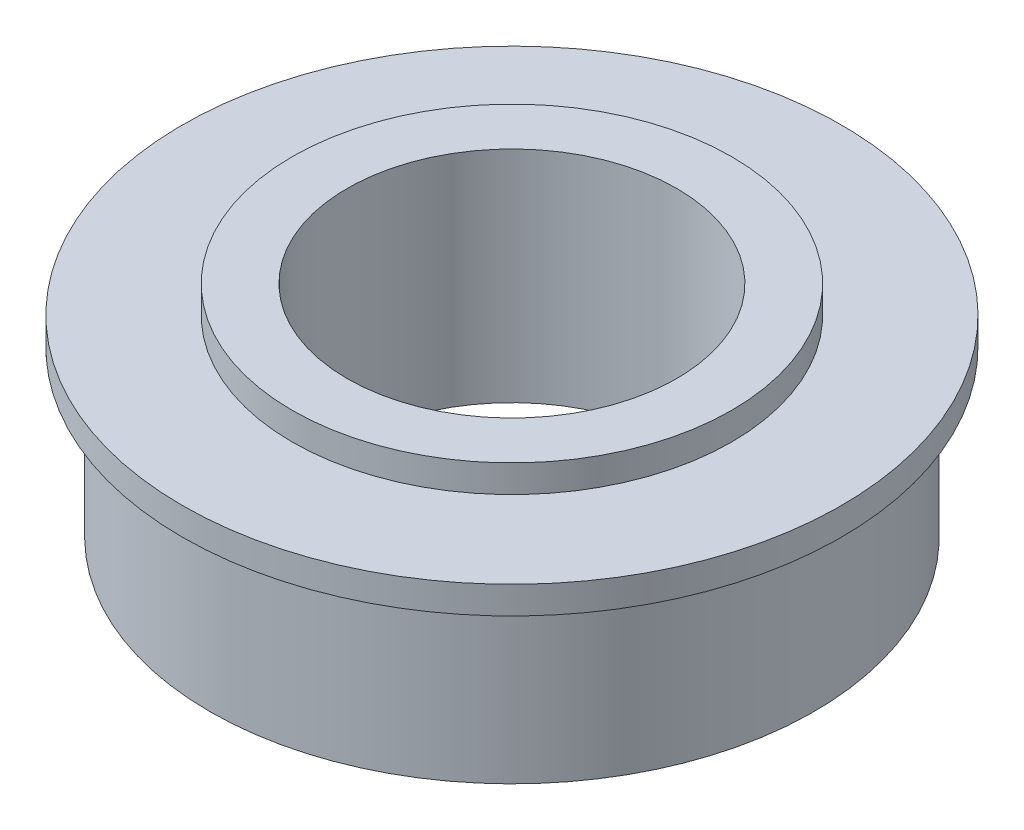
SolidWorks part; units mm, degrees
material "Chrome Stainless Steel"
ref_plane "Front Plane" through (0, 0, 0) normal (0, 0, 1) x (1, 0, 0)
ref_plane "Top Plane" through (0, 0, 0) normal (0, 1, 0) x (1, 0, 0)
ref_plane "Right Plane" through (0, 0, 0) normal (1, 0, 0) x (0, 0, -1)
sketch "Sketch1" plane through (0, 0, 0) normal (0, 0, 1) x (1, 0, 0)
  line L0 (9.525, 1.5875) -> (12.7, 1.5875)
  line L1 (12.7, 1.5875) -> (12.7, 0)
  line L2 (12.7, 0) -> (19.05, 0)
  line L3 (19.05, 0) -> (19.05, -1.5875)
  line L4 (19.05, -1.5875) -> (17.4625, -1.5875)
  line L5 (17.4625, -1.5875) -> (17.4625, -11.1125)
  line L6 (17.4625, -11.1125) -> (9.525, -11.1125)
  line L7 (9.525, -11.1125) -> (9.525, 1.5875)
  line L8 (0, 0) -> (0, -19.6393) construction
  line L9 (17.4625, -1.5875) -> (19.05, 0) construction
  dimension "D1" = 34.925
  dimension "D2" = 19.05
  dimension "D3" = 12.7
  dimension "D4" = 11.1125
  dimension "D5" = 38.1
  dimension "D6" = 45
  dimension "D7" = 3.175
  dimension "D8" = 9.525
revolve "Revolve1" add sketch "Sketch1" angle 360 about L8
